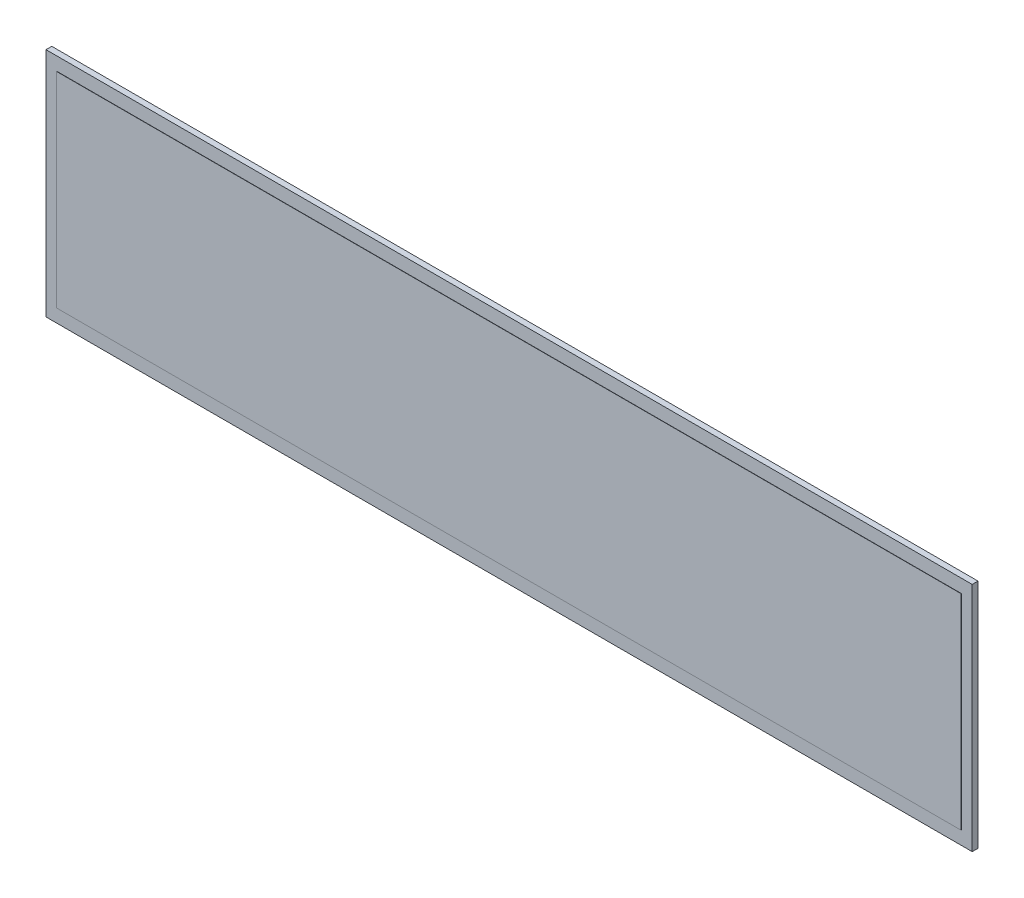
SolidWorks part; units mm, degrees
ref_plane "Front Plane" through (0, 0, 0) normal (0, 0, 1) x (1, 0, 0)
ref_plane "Top Plane" through (0, 0, 0) normal (0, 1, 0) x (1, 0, 0)
ref_plane "Right Plane" through (0, 0, 0) normal (1, 0, 0) x (0, 0, -1)
sketch "Sketch1" plane through (0, 0, 0) normal (0, 0, 1) x (1, 0, 0)
  line L1 (344.551, 86.106) -> (-344.551, 86.106)
  line L2 (344.551, 86.106) -> (344.551, -86.106)
  line L3 (344.551, -86.106) -> (-344.551, -86.106)
  line L4 (-344.551, 86.106) -> (-344.551, -86.106)
  line L5 (344.551, 86.106) -> (-344.551, -86.106) construction
  line L6 (344.551, -86.106) -> (-344.551, 86.106) construction
  point P0 (0, 0)
  dimension "D1" = 172.212
  dimension "D2" = 689.102
extrude "Boss-Extrude1" add sketch "Sketch1" along normal mid plane 4.318
sketch "Sketch2" plane through (0, 0, 2.159) normal (0, 0, 1) x (1, 0, 0)
  line L1 (336.55, 76.2) -> (-336.55, 76.2)
  line L2 (336.55, 76.2) -> (336.55, -76.2)
  line L3 (336.55, -76.2) -> (-336.55, -76.2)
  line L4 (-336.55, 76.2) -> (-336.55, -76.2)
  line L5 (336.55, 76.2) -> (-336.55, -76.2) construction
  line L6 (336.55, -76.2) -> (-336.55, 76.2) construction
  point P0 (0, 0)
  dimension "D1" = 673.1
  dimension "D2" = 152.4
extrude "Boss-Extrude2" add sketch "Sketch2" along normal blind 0.2032
